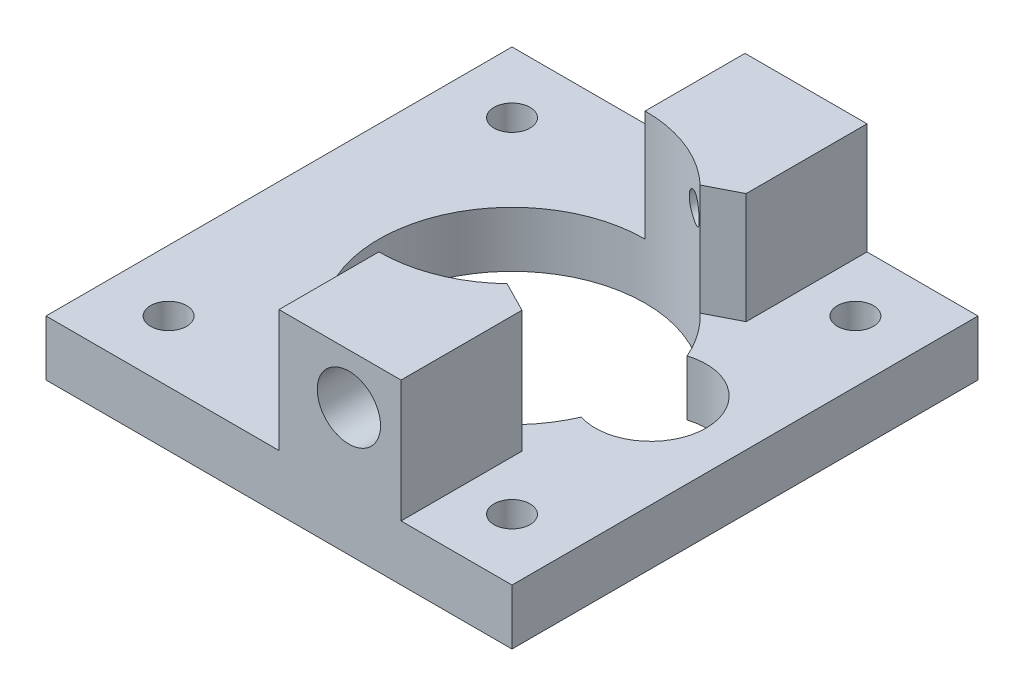
SolidWorks part; units mm, degrees
ref_plane "Front Plane" through (0, 0, 0) normal (0, 0, 1) x (1, 0, 0)
ref_plane "Top Plane" through (0, 0, 0) normal (0, 1, 0) x (1, 0, 0)
ref_plane "Right Plane" through (0, 0, 0) normal (1, 0, 0) x (0, 0, -1)
sketch "Sketch1" plane through (0, 0, 0) normal (0, 1, 0) x (1, 0, 0)
  line L1 (-21, 21) -> (21, 21)
  line L2 (-21, 21) -> (-21, -21)
  line L3 (-21, -21) -> (21, -21)
  line L4 (21, 21) -> (21, -21)
  line L5 (-21, 21) -> (21, -21) construction
  line L6 (-21, -21) -> (21, 21) construction
  circle A0 centre (0, 0) radius 12
  point P0 (0, 0)
  dimension "D3" = 24
  dimension "D1" = 42
  dimension "D2" = 42
extrude "Boss-Extrude1" add sketch "Sketch1" along normal blind 5
sketch "Sketch2" plane through (0, 5, 0) normal (0, 1, 0) x (1, 0, 0)
  line L0 (0, 21) -> (0, -3.2364) construction
  line L1 (21, 21) -> (-21, 21) construction
  line L2 (-21, 0) -> (-16.0173, 0) construction
  line L3 (-21, 21) -> (-21, -21) construction
  circle A0 centre (-15.475, 15.475) radius 1.625
  circle A1 centre (15.475, 15.475) radius 1.625
  circle A2 centre (15.475, -15.475) radius 1.625
  circle A3 centre (-15.475, -15.475) radius 1.625
  point P11 (-15.475, 17.1)
  point P12 (-17.1, 15.475)
  dimension "D1" = 3.25
  dimension "D2" = 3.9
  dimension "D3" = 3.9
extrude "Cut-Extrude1" cut sketch "Sketch2" against normal blind 8
sketch "Sketch3" plane through (0, 5, 0) normal (0, 1, 0) x (1, 0, 0)
  line L0 (0, 12) -> (0, 21)
  line L1 (8.2604, 8.7044) -> (11, 10.1029)
  line L2 (21, 0) -> (14.5439, 0) construction
  line L3 (21, -21) -> (21, 21) construction
  line L4 (21, 21) -> (-21, 21) construction
  line L5 (0, 21) -> (11, 21)
  line L6 (11, 21) -> (11, 10.1029)
  line L10 (0, -21) -> (11, -21)
  line L11 (0, -12) -> (0, -21)
  line L12 (11, -21) -> (11, -10.1029)
  line L13 (8.2604, -8.7044) -> (11, -10.1029)
  arc A0 (0, -12) -> (8.2604, -8.7044) centre (0, 0) ccw
  circle A1 centre (0, 0) radius 12 construction
  arc A2 (0, 12) -> (8.2604, 8.7044) centre (0, 0) cw
  dimension "D1" = 10
extrude "Boss-Extrude2" add sketch "Sketch3" along normal blind 10
sketch "Sketch4" plane through (0, 0, 21) normal (0, 0, 1) x (1, 0, 0)
  line L0 (11, 15) -> (11, 5) construction
  line L1 (0, 15) -> (11, 15) construction
  circle A0 centre (6.3, 11.5) radius 1.175
  dimension "D1" = 2.35
  dimension "D2" = 4.7
  dimension "D3" = 3.5
extrude "Cut-Extrude2" cut sketch "Sketch4" against normal up to surface (42 mm away) up to face at (2.75, 6.25, -21)
sketch "Sketch5" plane through (0, 5, 0) normal (0, 1, 0) x (1, 0, 0)
  line L0 (21, 0) -> (12.5, 0) construction
  line L1 (21, -21) -> (21, 21) construction
  circle A0 centre (12.5, 0) radius 5
  dimension "D2" = 10
  dimension "D1" = 8.5
extrude "Cut-Extrude3" cut sketch "Sketch5" against normal blind 10
sketch "Sketch6" plane through (0, 0, 21) normal (0, 0, 1) x (1, 0, 0)
  circle A0 centre (6.3, 11.5) radius 2.85
  dimension "D1" = 5.7
extrude "Cut-Extrude4" cut sketch "Sketch6" against normal blind 5
sketch "Sketch7" plane through (0, 15, 0) normal (0, 1, 0) x (1, 0, 0)
  line L0 (0, -21) -> (11, -21)
  line L1 (11, -21) -> (11, -10.1029)
  line L2 (11, -10.1029) -> (8.2604, -8.7044)
  line L3 (0, -21) -> (0, -12)
  arc A0 (0, -12) -> (8.2604, -8.7044) centre (0, 0) ccw
extrude "Boss-Extrude3" add sketch "Sketch7" along normal blind 1
